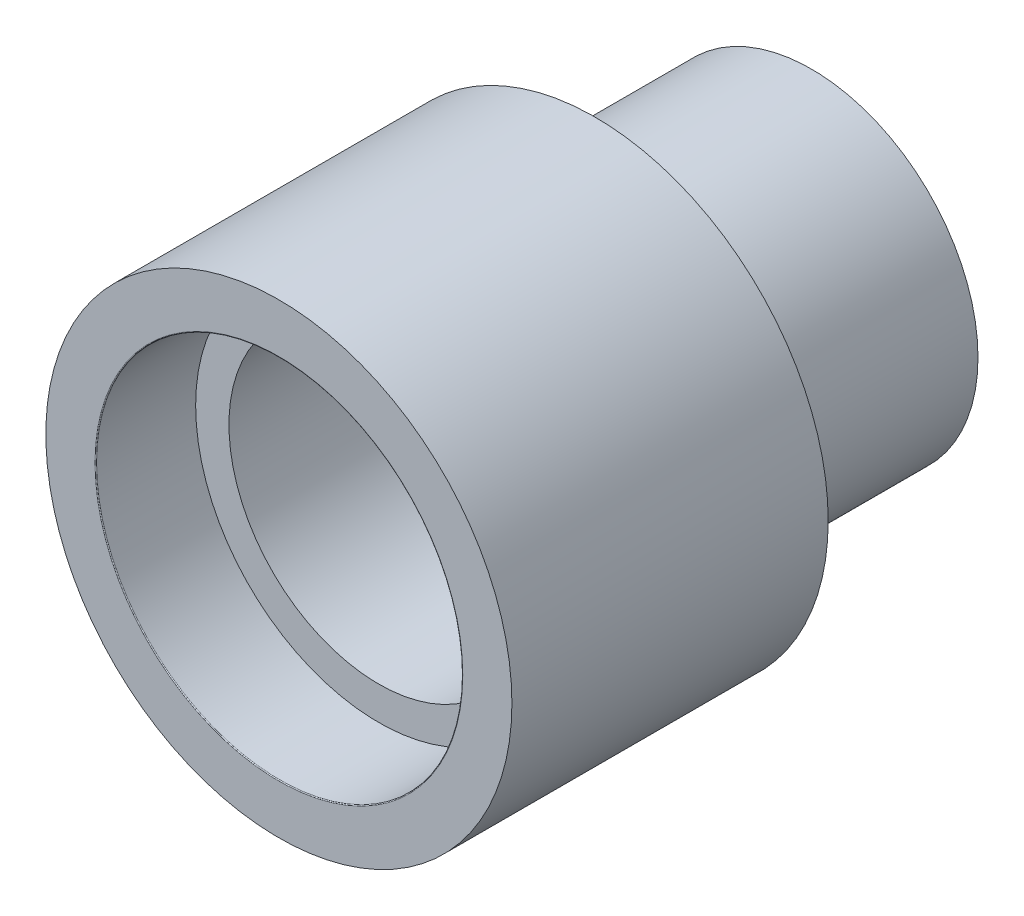
SolidWorks part; units mm, degrees
ref_plane "Front Plane" through (0, 0, 0) normal (0, 0, 1) x (1, 0, 0)
ref_plane "Top Plane" through (0, 0, 0) normal (0, 1, 0) x (1, 0, 0)
ref_plane "Right Plane" through (0, 0, 0) normal (1, 0, 0) x (0, 0, -1)
sketch "Sketch2" plane through (0, 0, 0) normal (0, 0, 1) x (1, 0, 0)
  circle A0 centre (0, 0) radius 10
  dimension "D1" = 20
extrude "Boss-Extrude1" add sketch "Sketch2" against normal blind 13
sketch "Sketch3" plane through (0, 0, 0) normal (0, 0, 1) x (1, 0, 0)
  circle A0 centre (0, 0) radius 14
  dimension "D1" = 28
extrude "Boss-Extrude2" add sketch "Sketch3" along normal blind 19
sketch "Sketch4" plane through (0, 0, 19) normal (0, 0, 1) x (1, 0, 0)
  circle A0 centre (0, 0) radius 11
  dimension "D1" = 22
extrude "Cut-Extrude1" cut sketch "Sketch4" against normal blind 6
sketch "Sketch5" plane through (0, 0, 13) normal (0, 0, 1) x (1, 0, 0)
  circle A0 centre (0, 0) radius 9
  dimension "D1" = 18
extrude "Cut-Extrude2" cut sketch "Sketch5" against normal blind 10
sketch "Sketch6" plane through (0, 0, -13) normal (0, 0, -1) x (-1, 0, 0)
  circle A0 centre (0, 0) radius 5
  dimension "D1" = 10
extrude "Cut-Extrude3" cut sketch "Sketch6" against normal through all
fillet "Fillet1" radius 0.05 1 edges at (11, 0, 19)
